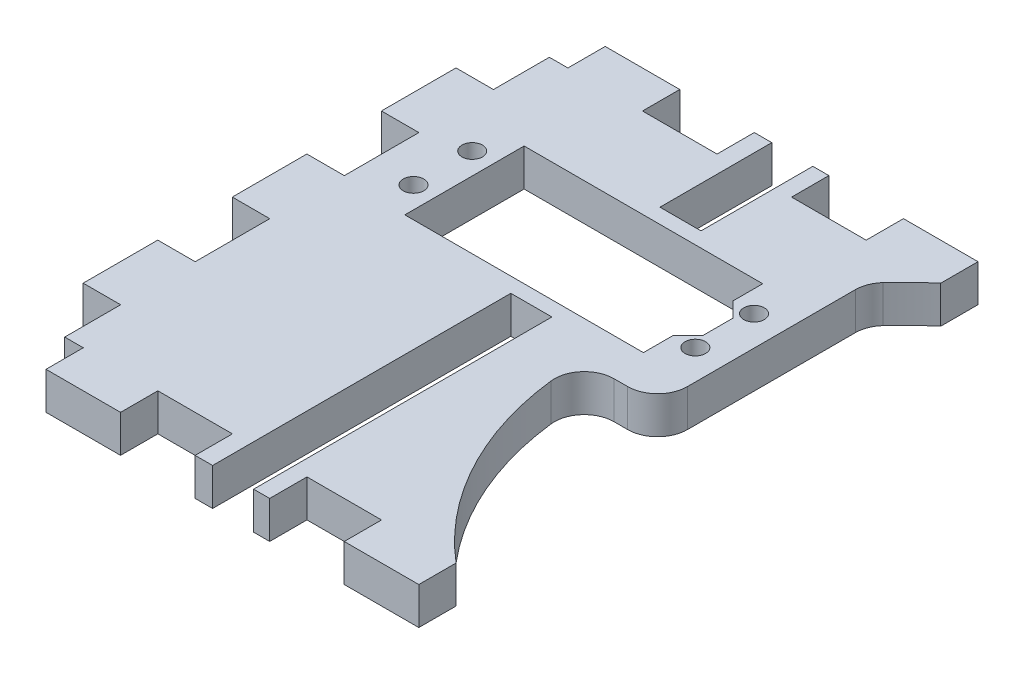
SolidWorks part; units mm, degrees
ref_plane "Front Plane" through (0, 0, 0) normal (0, 0, 1) x (1, 0, 0)
ref_plane "Top Plane" through (0, 0, 0) normal (0, 1, 0) x (1, 0, 0)
ref_plane "Right Plane" through (0, 0, 0) normal (1, 0, 0) x (0, 0, -1)
sketch "Sketch1" plane through (0, 0, 0) normal (0, 0, 1) x (1, 0, 0)
  line L0 (0, 0) -> (40.3547, 419.1) construction
  line L1 (40.3547, 419.1) -> (159.2585, 419.1) construction
  line L2 (159.2585, 419.1) -> (159.2585, 0) construction
  line L3 (159.2585, 0) -> (0, 0) construction
  line L4 (159.2585, -1000) -> (159.2585, 49000) construction
  line L5 (2.0164, 20.9415) -> (40.3547, 419.1) construction
  line L6 (2.0164, 20.9415) -> (41.8323, 17.1077) construction
  line L7 (40.3547, 419.1) -> (80.1706, 415.2662) construction
  line L8 (41.8323, 17.1077) -> (80.1706, 415.2662) construction
  line L9 (64.0085, -1000) -> (64.0085, 49000) construction
  line L10 (-42.7214, 317.5) -> (-118.5706, 324.8034) construction
  line L11 (-20.0013, 414.3375) -> (40.196, 414.3375) construction
  line L12 (-1162.1335, 304.8) -> (48837.8665, 304.8) construction
  line L13 (-120.1415, 292.1) -> (-43.9415, 292.1) construction
  line L14 (-118.5706, 324.8034) -> (-43.9415, 292.1) construction
  line L15 (-42.7214, 317.5) -> (-120.1415, 292.1) construction
  line L16 (40.196, 338.1375) -> (-20.0013, 338.1375) construction
  line L17 (-128.0517, 325.7164) -> (29.8985, 310.5075)
  line L18 (-128.0517, 325.7164) -> (-127.4431, 332.0371)
  line L19 (-127.4431, 332.0371) -> (40.3547, 419.1)
  line L20 (40.3547, 419.1) -> (108.4585, 419.1)
  line L21 (108.4585, 419.1) -> (108.4585, 0) construction
  line L22 (29.8985, 310.5075) -> (0.4102, 4.2603)
  line L23 (0.4102, 4.2603) -> (44.6556, 0)
  line L24 (44.6556, 0) -> (108.4585, 0)
  line L25 (108.4585, 419.1) -> (159.2585, 311.15)
  line L26 (159.2585, 311.15) -> (159.2585, 304.8)
  line L27 (159.2585, 304.8) -> (108.4585, 280.8941)
  line L28 (108.4585, 280.8941) -> (108.4585, 0)
  line L29 (4.0811, 42.3843) -> (3.4111, 35.4257) construction
  line L30 (4.0811, 42.3843) -> (48.5754, 38.1) construction
  line L31 (3.4111, 35.4257) -> (47.9053, 31.1414) construction
  line L32 (48.5754, 38.1) -> (47.9053, 31.1414) construction
  line L33 (3.7272, 38.7086) -> (10.048, 38.1) construction
  arc A0 (-118.5706, 324.8034) -> (-20.0013, 414.3375) centre (-20.0013, 315.3123) cw construction
  arc A1 (73.5335, 304.8) -> (40.196, 338.1375) centre (40.196, 304.8) ccw construction
  arc A2 (149.7335, 304.8) -> (40.196, 414.3375) centre (40.196, 304.8) ccw construction
  arc A3 (-42.7214, 317.5) -> (-20.0013, 338.1375) centre (-20.0013, 315.3123) cw construction
  point P7 (57.6585, 400.05)
  point P10 (41.5845, 31.75)
  point P17 (149.7335, 304.8)
  point P18 (73.5335, 304.8)
  dimension "D9" = 9.525
  dimension "D14" = 25.4
  dimension "D1" = 419.1
  dimension "D2" = 101.6
  dimension "D3" = 19.05
  dimension "D4" = 19.05
  dimension "D5" = 84.5
  dimension "D6" = 40
  dimension "D7" = 400
  dimension "D8" = 95.25
  dimension "D10" = 9.525
  dimension "D11" = 114.3
  dimension "D12" = 76.2
  dimension "D13" = 9.525
  dimension "D15" = 127
  dimension "D16" = 9.525
  dimension "D17" = 203.2
  dimension "D18" = 6.35
  dimension "D19" = 50.8
  dimension "D20" = 44.45
  dimension "D21" = 6.35
  dimension "D22" = 44.7
  dimension "D23" = 31.75
  dimension "D24" = 38.1
  dimension "D25" = 6.35
  dimension "D26" = 38.1
  dimension "D27" = 6.35
sketch "Sketch2" plane through (0, 0, 0) normal (0, 0, 1) x (1, 0, 0)
  line L0 (29.8985, 310.5075) -> (0.4102, 4.2603) construction
  line L1 (76.7085, 38.1) -> (3.6686, 38.1)
  line L2 (76.7085, 38.1) -> (76.7085, 31.75)
  line L3 (76.7085, 31.75) -> (3.6686, 31.75)
  line L4 (3.6686, 38.1) -> (3.6686, 31.75)
  line L6 (44.6556, 0) -> (108.4585, 0) construction
  line L8 (64.0085, -201000) -> (64.0085, 249000) construction
  dimension "D1" = 6.35
  dimension "D2" = 12.7
  dimension "D3" = 31.75
extrude "Boss-Extrude1" add sketch "Sketch2" along normal blind 95.25 contours L1 L4 L3 L2
sketch "Sketch3" plane through (0, 38.1, 0) normal (0, 1, 0) x (1, 0, 0)
  line L2 (64.1685, -29.21) -> (64.1685, -34.29)
  line L3 (20.9885, -41.91) -> (61.6285, -41.91)
  line L4 (20.9885, -41.91) -> (20.9885, -21.59)
  line L5 (20.9885, -21.59) -> (61.6285, -21.59)
  line L6 (61.6285, -41.91) -> (61.6285, -21.59) construction
  line L7 (20.9885, -41.91) -> (61.6285, -21.59) construction
  line L8 (20.9885, -21.59) -> (61.6285, -41.91) construction
  line L9 (17.3085, -36.75) -> (65.3085, -36.75) construction
  line L10 (17.3085, -36.75) -> (17.3085, -26.75) construction
  line L11 (17.3085, -26.75) -> (65.3085, -26.75) construction
  line L12 (65.3085, -36.75) -> (65.3085, -26.75) construction
  line L13 (17.3085, -36.75) -> (65.3085, -26.75) construction
  line L14 (17.3085, -26.75) -> (65.3085, -36.75) construction
  line L15 (64.1685, -31.75) -> (41.3085, -31.75) construction
  line L16 (61.6285, -21.59) -> (61.6285, -26.67)
  line L17 (61.6285, -26.67) -> (64.1685, -29.21)
  line L18 (64.1685, -34.29) -> (61.6285, -36.83)
  line L19 (61.6285, -36.83) -> (61.6285, -41.91)
  line L21 (44.6556, 0) -> (108.4585, 0) construction
  circle A1 centre (17.3085, -26.75) radius 1.75
  circle A2 centre (17.3085, -36.75) radius 1.75
  circle A3 centre (65.3085, -36.75) radius 1.75
  circle A4 centre (65.3085, -26.75) radius 1.75
  point P0 (64.0085, 0)
  point P6 (41.3085, -31.75)
  point P11 (41.3085, -31.75)
  point P24 (51.3085, -31.75)
  dimension "D7" = 3.5
  dimension "D2" = 12.7
  dimension "D3" = 20.32
  dimension "D4" = 40.64
  dimension "D5" = 10
  dimension "D6" = 48
  dimension "D8" = 14
  dimension "D9" = 5.08
  dimension "D10" = 135
  dimension "D11" = 2.54
  dimension "D12" = 31.75
extrude "Cut-Extrude1" cut sketch "Sketch3" against normal through all
sketch "Sketch5" plane through (0, 0, 0) normal (0, 0, 1) x (1, 0, 0)
  line L0 (111.6335, 304.8) -> (111.6335, 38.1) construction
  line L1 (73.5335, 304.8) -> (149.7335, 304.8) construction
  line L2 (76.7085, 38.1) -> (3.6686, 38.1) construction
sketch "Sketch6" plane through (0, 38.1, 0) normal (0, 1, 0) x (1, 0, 0)
  line L0 (111.6335, 0) -> (111.6335, -47.625) construction
  line L1 (76.7085, -95.25) -> (76.7085, 0) construction
  line L2 (57.569, -48.26) -> (70.3885, -48.26)
  line L3 (70.3885, -48.26) -> (70.3885, -12.6646)
  line L4 (44.6556, 0) -> (108.4585, 0) construction
  line L5 (20.9885, -41.91) -> (61.6285, -41.91) construction
  line L6 (76.7085, -6.35) -> (76.7085, -88.9)
  arc A0 (76.7085, -88.9) -> (57.569, -48.26) centre (111.6335, -47.625) cw
  arc A1 (70.3885, -12.6646) -> (76.7085, -6.35) centre (111.6335, -47.625) cw
  circle A2 centre (65.3085, -26.75) radius 1.75 construction
  dimension "D4" = 5.08
  dimension "D1" = 47.625
  dimension "D2" = 6.35
  dimension "D3" = 6.35
  dimension "D5" = 6.35
extrude "Cut-Extrude2" cut sketch "Sketch6" against normal through all
fillet "Fillet1" radius 5.08 3 edges at (70.3885, 34.925, 12.6646) (70.3885, 34.925, 48.26) (57.569, 34.925, 48.26)
sketch "Sketch8" plane through (0, 38.1, 0) normal (0, 1, 0) x (1, 0, 0)
  line L0 (76.7085, -95.25) -> (3.6686, -95.25) construction
  line L1 (41.5845, 0) -> (48.5754, 0)
  line L2 (41.5845, 0) -> (41.5845, -19.05)
  line L3 (41.5845, -19.05) -> (48.5754, -19.05)
  line L4 (48.5754, 0) -> (48.5754, -19.05)
  line L5 (41.5845, -95.25) -> (48.5754, -95.25)
  line L6 (41.5845, -95.25) -> (41.5845, -44.45)
  line L7 (41.5845, -44.45) -> (48.5754, -44.45)
  line L8 (48.5754, -95.25) -> (48.5754, -44.45)
  line L9 (45.08, -19.05) -> (45.08, -44.45) construction
  line L10 (45.08, -31.75) -> (20.9885, -31.75) construction
  line L11 (20.9885, -21.59) -> (20.9885, -41.91) construction
  dimension "D1" = 25.4
extrude "Cut-Extrude3" cut sketch "Sketch8" against normal through all
sketch "Sketch9" plane through (0, 38.1, 0) normal (0, 1, 0) x (1, 0, 0)
  line L0 (76.7085, 0) -> (48.5754, 0) construction
  line L1 (64.0085, 0) -> (51.3085, 0)
  line L2 (64.0085, 0) -> (64.0085, -6.35)
  line L3 (64.0085, -6.35) -> (51.3085, -6.35)
  line L4 (51.3085, 0) -> (51.3085, -6.35)
  line L5 (76.7085, -95.25) -> (48.5754, -95.25) construction
  line L6 (64.0085, -95.25) -> (51.3085, -95.25)
  line L7 (64.0085, -95.25) -> (64.0085, -88.9)
  line L8 (64.0085, -88.9) -> (51.3085, -88.9)
  line L9 (51.3085, -95.25) -> (51.3085, -88.9)
  line L10 (76.7085, -6.35) -> (76.7085, 0) construction
  dimension "D1" = 12.7
  dimension "D2" = 12.7
  dimension "D3" = 6.35
  dimension "D4" = 12.7
extrude "Cut-Extrude4" cut sketch "Sketch9" against normal through all
pattern_linear "LPattern1" count 8 spacing 25.4 along (-1, 0, 0) of "Cut-Extrude4"
sketch "Sketch10" plane through (0, 38.1, 0) normal (0, 1, 0) x (1, 0, 0)
  line L0 (3.6686, -88.9) -> (3.6686, -6.35) construction
  line L1 (3.6686, -15.875) -> (10.048, -15.875)
  line L2 (3.6686, -15.875) -> (3.6686, 0)
  line L3 (3.6686, 0) -> (10.048, 0)
  line L4 (10.048, -15.875) -> (10.048, 0)
  line L5 (25.9085, 0) -> (13.2085, 0) construction
  line L6 (25.9085, -95.25) -> (13.2085, -95.25) construction
  line L7 (3.6686, -95.25) -> (10.048, -95.25)
  line L8 (3.6686, -95.25) -> (3.6686, -79.375)
  line L9 (3.6686, -79.375) -> (10.048, -79.375)
  line L10 (10.048, -95.25) -> (10.048, -79.375)
  line L11 (3.6686, -66.675) -> (10.048, -66.675)
  line L12 (3.6686, -66.675) -> (3.6686, -53.975)
  line L13 (3.6686, -53.975) -> (10.048, -53.975)
  line L14 (10.048, -66.675) -> (10.048, -53.975)
  line L15 (3.6686, -41.275) -> (10.048, -41.275)
  line L16 (3.6686, -41.275) -> (3.6686, -28.575)
  line L17 (3.6686, -28.575) -> (10.048, -28.575)
  line L18 (10.048, -41.275) -> (10.048, -28.575)
  dimension "D2" = 12.7
  dimension "D3" = 12.7
  dimension "D4" = 12.7
  dimension "D5" = 12.7
  dimension "D6" = 12.7
extrude "Cut-Extrude5" cut sketch "Sketch10" against normal through all
